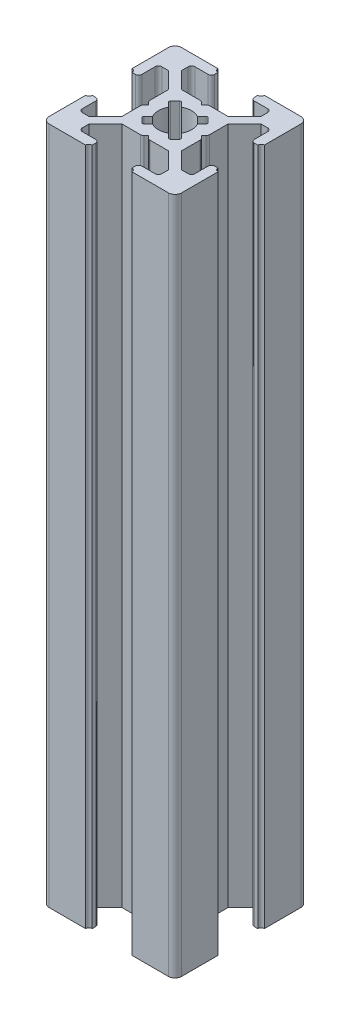
SolidWorks part; units mm, degrees
ref_plane "Front Plane" through (0, 0, 0) normal (0, 0, 1) x (1, 0, 0)
ref_plane "Top Plane" through (0, 0, 0) normal (0, 1, 0) x (1, 0, 0)
ref_plane "Right Plane" through (0, 0, 0) normal (1, 0, 0) x (0, 0, -1)
sketch "Sketch3" plane through (0, 0, 0) normal (0, 1, 0) x (1, 0, 0)
  line L0 (7, 20) -> (7, 18.5)
  line L1 (0, 0) -> (20, 0)
  line L2 (0, 0) -> (0, 20)
  line L3 (0, 20) -> (20, 20)
  line L4 (20, 0) -> (20, 20)
  line L5 (7, 18.5) -> (4, 18.5)
  line L6 (4, 18.5) -> (4, 17)
  line L7 (4, 17) -> (6.5, 14.5)
  line L8 (6.5, 14.5) -> (13.5, 14.5)
  line L9 (13.5, 14.5) -> (16, 17)
  line L10 (16, 17) -> (16, 18.5)
  line L11 (16, 18.5) -> (13, 18.5)
  line L12 (13, 18.5) -> (13, 20)
  line L13 (13, 20) -> (7, 20)
  line L14 (9.5, 14.5) -> (10, 14)
  line L15 (10, 14) -> (10.5, 14.5)
  line L16 (10.5, 14.5) -> (9.5, 14.5)
  line L17 (13, 19.5) -> (13, 20)
  line L18 (13.5, 20) -> (13, 20)
  line L19 (7, 19.5) -> (7, 20)
  line L20 (6.5, 20) -> (7, 20)
  line L21 (0, 13) -> (1.5, 13)
  line L22 (1.5, 13) -> (1.5, 16)
  line L23 (1.5, 16) -> (3, 16)
  line L24 (3, 16) -> (5.5, 13.5)
  line L25 (5.5, 13.5) -> (5.5, 6.5)
  line L26 (5.5, 6.5) -> (3, 4)
  line L27 (3, 4) -> (1.5, 4)
  line L28 (1.5, 4) -> (1.5, 7)
  line L29 (1.5, 7) -> (0, 7)
  line L30 (0, 7) -> (0, 13)
  line L31 (5.5, 10.5) -> (5.5, 9.5)
  line L32 (5.5, 9.5) -> (6, 10)
  line L33 (6, 10) -> (5.5, 10.5)
  line L34 (0.5, 13) -> (0, 13)
  line L35 (0, 13.5) -> (0, 13)
  line L36 (0, 6.5) -> (0, 7)
  line L37 (0.5, 7) -> (0, 7)
  line L38 (10, 20) -> (10, 0) construction
  line L39 (20, 10) -> (0, 10) construction
  line L40 (10, 6) -> (10.5, 5.5)
  line L41 (9.5, 5.5) -> (10, 6)
  line L42 (10.5, 5.5) -> (9.5, 5.5)
  line L43 (13.5, 0) -> (13, 0)
  line L44 (13, 0.5) -> (13, 0)
  line L45 (6.5, 0) -> (7, 0)
  line L46 (7, 0.5) -> (7, 0)
  line L47 (13, 1.5) -> (13, 0)
  line L48 (16, 1.5) -> (13, 1.5)
  line L49 (16, 3) -> (16, 1.5)
  line L50 (13.5, 5.5) -> (16, 3)
  line L51 (6.5, 5.5) -> (13.5, 5.5)
  line L52 (4, 3) -> (6.5, 5.5)
  line L53 (4, 1.5) -> (4, 3)
  line L54 (7, 1.5) -> (4, 1.5)
  line L55 (7, 0) -> (7, 1.5)
  line L56 (13, 0) -> (7, 0)
  line L57 (14.5, 9.5) -> (14, 10)
  line L58 (14.5, 10.5) -> (14.5, 9.5)
  line L59 (14, 10) -> (14.5, 10.5)
  line L60 (19.5, 7) -> (20, 7)
  line L61 (20, 6.5) -> (20, 7)
  line L62 (20, 13.5) -> (20, 13)
  line L63 (19.5, 13) -> (20, 13)
  line L64 (18.5, 7) -> (20, 7)
  line L65 (18.5, 4) -> (18.5, 7)
  line L66 (17, 4) -> (18.5, 4)
  line L67 (14.5, 6.5) -> (17, 4)
  line L68 (14.5, 13.5) -> (14.5, 6.5)
  line L69 (17, 16) -> (14.5, 13.5)
  line L70 (18.5, 16) -> (17, 16)
  line L71 (18.5, 13) -> (18.5, 16)
  line L72 (20, 13) -> (18.5, 13)
  line L73 (20, 7) -> (20, 13)
  arc A0 (13.5, 20) -> (13, 19.5) centre (13, 20) cw
  arc A1 (6.5, 20) -> (7, 19.5) centre (7, 20) ccw
  arc A2 (0.5, 13) -> (0, 13.5) centre (0, 13) ccw
  arc A3 (0.5, 7) -> (0, 6.5) centre (0, 7) cw
  arc A4 (13.5, 0) -> (13, 0.5) centre (13, 0) ccw
  arc A5 (6.5, 0) -> (7, 0.5) centre (7, 0) cw
  arc A6 (19.5, 7) -> (20, 6.5) centre (20, 7) ccw
  arc A7 (19.5, 13) -> (20, 13.5) centre (20, 13) cw
  point P7 (10, 14.5)
  point P16 (10, 20)
  point P26 (5.5, 10)
  point P35 (0, 10)
  dimension "D16" = 0.5
  dimension "D17" = 0.5
  dimension "D28" = 0.5
  dimension "D29" = 0.5
  dimension "D1" = 20
  dimension "D2" = 20
  dimension "D3" = 7
  dimension "D4" = 7
  dimension "D5" = 1.5
  dimension "D6" = 1.5
  dimension "D7" = 3
  dimension "D8" = 3
  dimension "D9" = 1.5
  dimension "D10" = 1.5
  dimension "D11" = 7
  dimension "D12" = 5.5
  dimension "D13" = 0.5
  dimension "D14" = 0.5
  dimension "D15" = 0.5
  dimension "D18" = 7
  dimension "D19" = 7
  dimension "D20" = 1.5
  dimension "D21" = 1.5
  dimension "D22" = 3
  dimension "D23" = 7
  dimension "D24" = 5.5
  dimension "D25" = 0.5
  dimension "D26" = 0.5
  dimension "D27" = 0.5
extrude "Boss-Extrude1" add sketch "Sketch3" along normal blind 102.5 contours L72 A7 L4 L3 A0 L12 L11 L10 L9 L8 L15 L14 L7 L6 L5 L0 A1 L2 A2 L21 L22 L23 L24 L25 L33 L32 L26 L27 L28 L29 A3 L1 A5 L55 L54 L53 L52 L51 L41 L40 L50 L49 L48 L47 A4
fillet "Fillet1" radius 1 4 edges at (0, 51.25, 0) (20, 51.25, 0) (20, 51.25, -20) (0, 51.25, -20)
sketch "Sketch4" plane through (0, 102.5, 0) normal (0, 1, 0) x (1, 0, 0)
  line L0 (13.5, 14.5) -> (5.5, 6.5) construction
  line L1 (14.5, 13.5) -> (6.5, 5.5) construction
  line L2 (10.5, 14.5) -> (14.5, 10.5) construction
  line L3 (12, 13) -> (13, 12)
  line L4 (13, 12) -> (8, 7)
  line L5 (8, 7) -> (7, 8)
  line L6 (7, 8) -> (12, 13)
  line L7 (13.5, 14.5) -> (16, 17) construction
  line L8 (17, 16) -> (14.5, 13.5) construction
  line L9 (5.5, 9.5) -> (9.5, 5.5) construction
  line L10 (5.5, 10.5) -> (9.5, 14.5) construction
  line L11 (14.5, 9.5) -> (10.5, 5.5) construction
  line L12 (6.5, 14.5) -> (14.5, 6.5) construction
  line L13 (5.5, 13.5) -> (13.5, 5.5) construction
  line L14 (7, 12) -> (8, 13)
  line L15 (8, 13) -> (13, 8)
  line L16 (13, 8) -> (12, 7)
  line L17 (12, 7) -> (7, 12)
  line L18 (4, 17) -> (6.5, 14.5) construction
  line L19 (3, 16) -> (5.5, 13.5) construction
  line L20 (20, 10) -> (0, 10) construction
  circle A0 centre (10, 10) radius 2.5
  dimension "D1" = 5
extrude "Cut-Extrude1" cut sketch "Sketch4" against normal through all contours L6 A0 L15 | L4 A0 L6 L15 | L15 A0 L17 L6 | L17 L4 L15 L6 | L17 A0 L6 | L6 A0 L4 L17 | L4 A0 L17 | L17 A0 L15 L4 | L15 A0 L4 | A0 L6 L5 L4 | A0 L17 L16 L15 | A0 L4 L3 L6 | A0 L15 L14 L17
fillet "Fillet2" radius 0.5 24 edges at (1.5, 51.25, -16) (1.5, 51.25, -13) (5.5, 51.25, -10.5) (5.5, 51.25, -9.5) (1.5, 51.25, -7) (1.5, 51.25, -4) (4, 51.25, -1.5) (7, 51.25, -1.5) (9.5, 51.25, -5.5) (10.5, 51.25, -5.5) (13, 51.25, -1.5) (16, 51.25, -1.5) (18.5, 51.25, -4) (18.5, 51.25, -7) (18.5, 51.25, -13) (18.5, 51.25, -16) (14.5, 51.25, -9.5) (14.5, 51.25, -10.5) (10.5, 51.25, -14.5) (9.5, 51.25, -14.5) (16, 51.25, -18.5) (13, 51.25, -18.5) (7, 51.25, -18.5) (4, 51.25, -18.5)
fillet "Fillet3" radius 0.25 8 edges at (13, 51.25, -8) (12, 51.25, -7) (13, 51.25, -12) (12, 51.25, -13) (8, 51.25, -13) (7, 51.25, -12) (7, 51.25, -8) (8, 51.25, -7)
